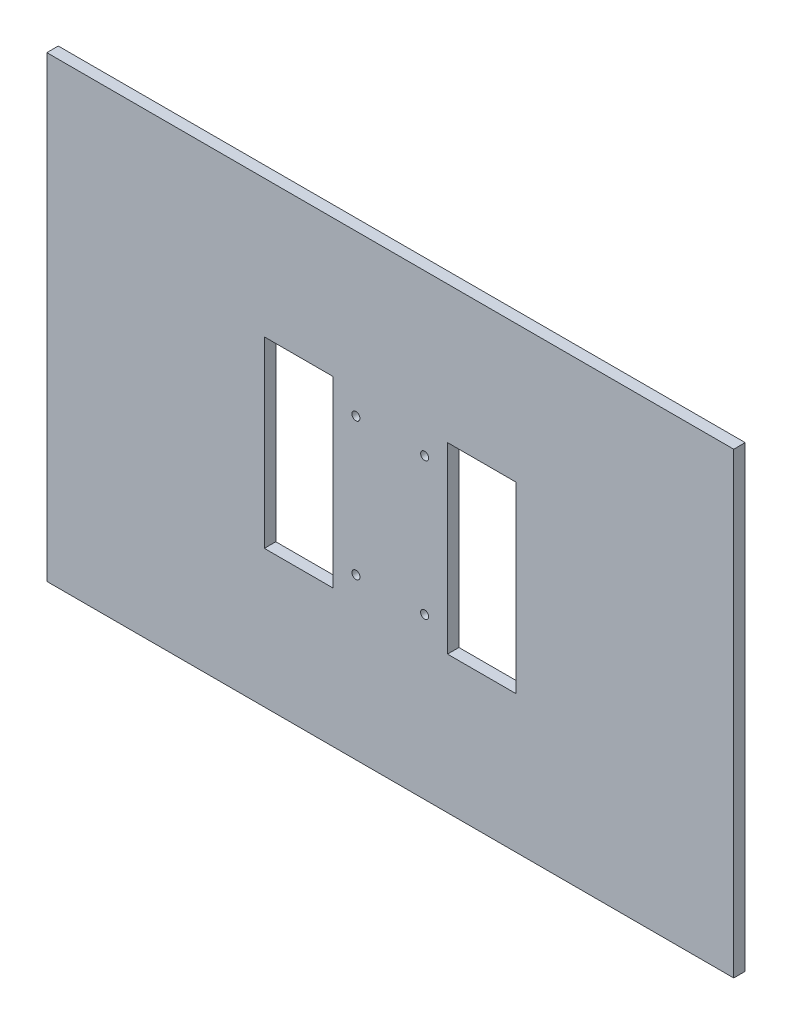
SolidWorks part; units mm, degrees
ref_plane "正面(Front)" through (0, 0, 0) normal (0, 0, 1) x (1, 0, 0)
ref_plane "平面(Top)" through (0, 0, 0) normal (0, 1, 0) x (1, 0, 0)
ref_plane "右側面(Right)" through (0, 0, 0) normal (1, 0, 0) x (0, 0, -1)
sketch "ｽｹｯﾁ1" plane through (0, 0, 0) normal (0, 0, 1) x (1, 0, 0)
  line L1 (-150, 100) -> (150, 100)
  line L2 (-150, 100) -> (-150, -100)
  line L3 (-150, -100) -> (150, -100)
  line L4 (150, 100) -> (150, -100)
  line L5 (-150, 100) -> (150, -100) construction
  line L6 (-150, -100) -> (150, 100) construction
  point P0 (0, 0)
  dimension "D1" = 300
  dimension "D2" = 200
extrude "ﾎﾞｽ - 押し出し1" add sketch "ｽｹｯﾁ1" along normal blind 5
sketch "ｽｹｯﾁ2" plane through (0, 0, 5) normal (0, 0, 1) x (1, 0, 0)
  line L0 (0, 0) -> (0, 114.4681) construction
  line L1 (-15, 30) -> (15, 30) construction
  line L2 (-15, 30) -> (-15, -30) construction
  line L3 (-15, -30) -> (15, -30) construction
  line L4 (15, 30) -> (15, -30) construction
  line L5 (-15, 30) -> (15, -30) construction
  line L6 (-15, -30) -> (15, 30) construction
  line L7 (55, -40) -> (25, -40)
  line L8 (-55, 40) -> (-25, 40)
  line L9 (-55, 40) -> (-55, -40)
  line L10 (-55, -40) -> (-25, -40)
  line L11 (-25, 40) -> (-25, -40)
  line L12 (-55, 40) -> (-25, -40) construction
  line L13 (-55, -40) -> (-25, 40) construction
  line L14 (25, 40) -> (25, -40)
  line L15 (55, 40) -> (25, 40)
  line L16 (55, 40) -> (55, -40)
  circle A0 centre (15, 30) radius 1.75
  circle A1 centre (-15, 30) radius 1.75
  circle A2 centre (-15, -30) radius 1.75
  circle A3 centre (15, -30) radius 1.75
  point P0 (0, 0)
  point P12 (-40, 0)
  point P17 (0, 0)
  dimension "D3" = 3.5
  dimension "D1" = 30
  dimension "D2" = 60
  dimension "D4" = 30
  dimension "D5" = 80
  dimension "D6" = 10
extrude "ｶｯﾄ - 押し出し1" cut sketch "ｽｹｯﾁ2" against normal through all
